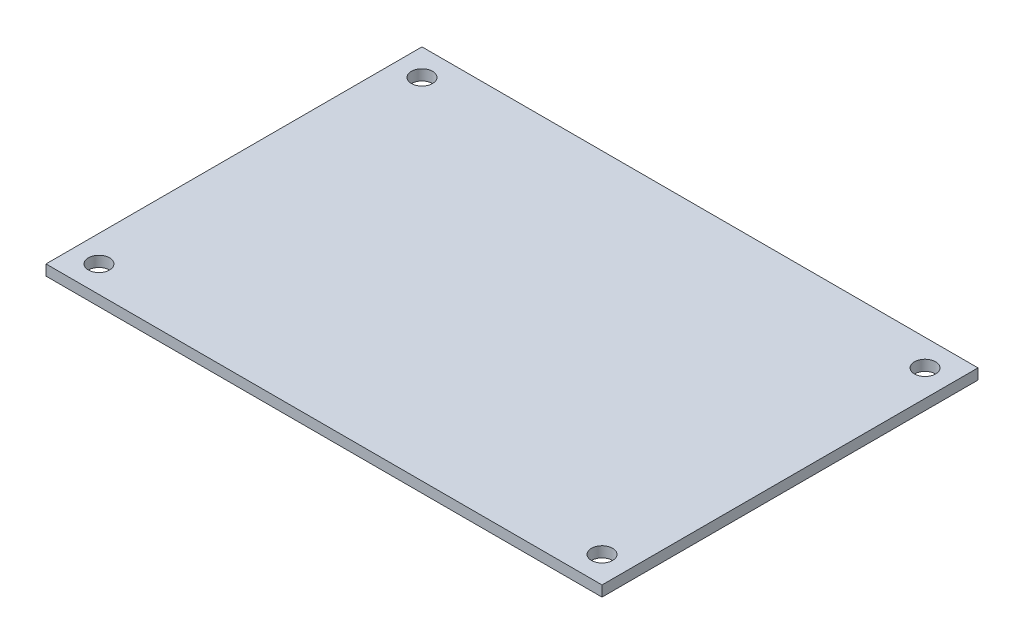
SolidWorks part; units mm, degrees
ref_plane "Front Plane" through (0, 0, 0) normal (0, 0, 1) x (1, 0, 0)
ref_plane "Top Plane" through (0, 0, 0) normal (0, 1, 0) x (1, 0, 0)
ref_plane "Right Plane" through (0, 0, 0) normal (1, 0, 0) x (0, 0, -1)
sketch "Sketch1" plane through (0, 0, 0) normal (0, 1, 0) x (1, 0, 0)
  line L1 (-52.5, -35.5) -> (52.5, -35.5)
  line L2 (-52.5, -35.5) -> (-52.5, 35.5)
  line L3 (-52.5, 35.5) -> (52.5, 35.5)
  line L4 (52.5, -35.5) -> (52.5, 35.5)
  line L5 (-52.5, -35.5) -> (52.5, 35.5) construction
  line L6 (-52.5, 35.5) -> (52.5, -35.5) construction
  circle A0 centre (-47.5, 30.5) radius 2
  circle A1 centre (47.5, 30.5) radius 2
  circle A2 centre (47.5, -30.5) radius 2
  circle A3 centre (-47.5, -30.5) radius 2
  point P0 (0, 0)
  dimension "D3" = 4
  dimension "D1" = 105
  dimension "D2" = 71
  dimension "D4" = 5
  dimension "D5" = 5
  dimension "D6" = 5
  dimension "D7" = 5
extrude "Boss-Extrude1" add sketch "Sketch1" along normal blind 2
